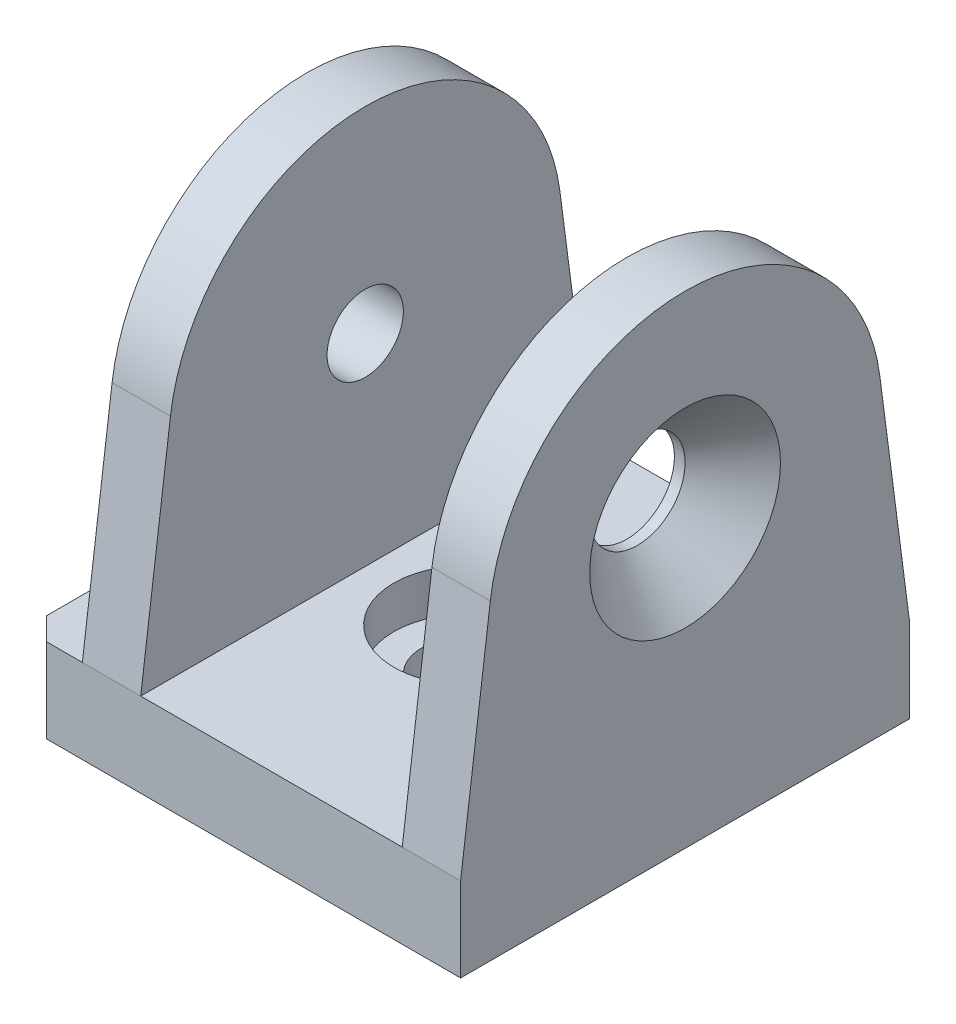
SolidWorks part; units mm, degrees
material "Алюминиевый сплав"
ref_plane "Спереди" through (0, 0, 0) normal (0, 0, 1) x (1, 0, 0)
ref_plane "Сверху" through (0, 0, 0) normal (0, 1, 0) x (1, 0, 0)
ref_plane "Справа" through (0, 0, 0) normal (1, 0, 0) x (0, 0, -1)
sketch "Эскиз1" plane through (0, 0, 0) normal (0, 1, 0) x (1, 0, 0)
  line L1 (19.45, -20) -> (-19.45, -20)
  line L2 (19.45, -20) -> (19.45, 20)
  line L3 (19.45, 20) -> (-19.45, 20)
  line L4 (-19.45, -20) -> (-19.45, 20)
  line L5 (19.45, -20) -> (-19.45, 20) construction
  line L6 (19.45, 20) -> (-19.45, -20) construction
  point P0 (0, 0)
  dimension "D1" = 38.9
  dimension "D2" = 40
extrude "Бобышка-Вытянуть1" add sketch "Эскиз1" along normal blind 7.5
sketch "Эскиз2" plane through (0, 0, 0) normal (0, 0, 1) x (1, 0, 0)
  line L1 (-19.45, 0) -> (19.45, 0) construction
  line L2 (-4, 0) -> (-4, 3.75)
  line L3 (-4, 3.75) -> (-6.5, 3.75)
  line L4 (-6.5, 3.75) -> (-6.5, 7.5)
  line L5 (-19.45, 7.5) -> (19.45, 7.5) construction
  line L7 (0, 7.5) -> (0, 0) construction
  line L11 (-19.45, 7.5) -> (-19.45, 0) construction
  line L12 (-6.5, 7.5) -> (0, 7.5)
  line L13 (0, 0) -> (-4, 0)
  line L14 (0, 0) -> (0, 7.5)
  point P17 (-19.45, 3.75)
  dimension "D1" = 8
  dimension "D2" = 13
revolve "Вырез-Повернуть1" cut sketch "Эскиз2" angle 360 about L7
sketch "Эскиз3" plane through (19.45, 0, 0) normal (1, 0, 0) x (0, 0, -1)
  line L0 (-20, 7.5) -> (-17.3526, 27.7667)
  line L1 (17.3526, 27.7667) -> (20, 7.5)
  line L2 (20, 7.5) -> (-20, 7.5)
  line L3 (-20, 0) -> (20, 0) construction
  arc A0 (-17.3526, 27.7667) -> (17.3526, 27.7667) centre (0, 25.5) cw
  dimension "D1" = 43
  dimension "D2" = 18
extrude "Бобышка-Вытянуть2" add sketch "Эскиз3" against normal blind 33.7
sketch "Эскиз4" plane through (0, 0, 0) normal (0, 0, 1) x (1, 0, 0)
  line L0 (-14.25, 7.5) -> (19.45, 7.5) construction
  line L1 (14.25, 7.5) -> (-9.05, 7.5)
  line L2 (14.25, 7.5) -> (14.25, 43)
  line L3 (14.25, 43) -> (-9.05, 43)
  line L4 (-9.05, 7.5) -> (-9.05, 43)
  line L5 (19.45, 43) -> (-14.25, 43) construction
  line L6 (14.25, 25.25) -> (19.45, 25.25) construction
  line L7 (19.45, 27.7667) -> (19.45, 7.5) construction
  line L8 (-9.05, 25.25) -> (-14.25, 25.25) construction
  line L9 (-14.25, 27.7667) -> (-14.25, 7.5) construction
  dimension "D1" = 5.2
extrude "Вырез-Вытянуть1" cut sketch "Эскиз4" against normal through all and the other way through all
chamfer "Фаска1" distance 2 angle 45 2 edges at (-19.45, 3.75, -20) (-19.45, 3.75, 20)
hole_wizard "Зенковка для винта с полупотайной головкой M81" positions "Эскиз8" profile "Эскиз10" countersink size "M8" standard "ISO" end condition up to next
sketch "Эскиз8" plane through (19.45, 0, 0) normal (1, 0, 0) x (0, 0, -1)
  point P0 (0, 25.5)
sketch "Эскиз10" plane through (19.45, 25.5, 0) normal (0, 1, 0) x (0, 0, -1)
  line L0 (0, 0) -> (0, 5.2)
  line L1 (0, 5.2) -> (4.25, 5.2)
  line L2 (4.25, 5.2) -> (4.25, 4.25)
  line L3 (4.25, 4.25) -> (8.5, 0)
  line L5 (8.5, 0) -> (0, 0)
  line L6 (-4.25, 4.25) -> (-8.5, 0) construction
  line L11 (0, -6.35) -> (0, 107.95) construction
  dimension "Диаметр сквозного отверстия" = 8.5
  dimension "Глубина сквозного отверстия" = 5.2
  dimension "Диаметр передней зенковки" = 17
  dimension "Угол передней зенковки" = 90
hole_wizard "Отверстие обработанное метчиком M81" positions "Эскиз11" profile "Эскиз13" tap size "M8" standard "ISO" end condition up to next
sketch "Эскиз11" plane through (-14.25, 0, 0) normal (-1, 0, 0) x (0, 0, 1)
  point P0 (0, 25.5)
sketch "Эскиз13" plane through (-14.25, 25.5, 0) normal (0, 1, 0) x (0, 0, 1)
  line L0 (0, 0) -> (0, 5.2)
  line L1 (0, 5.2) -> (3.4, 5.2)
  line L2 (3.4, 5.2) -> (3.4, 0)
  line L5 (3.4, 0) -> (0, 0)
  line L11 (0, -6.35) -> (0, 107.95) construction
  dimension "Диаметр проходного сверла" = 6.8
  dimension "Глубина проходного сверла" = 5.2
cosmetic thread "Отверстие резьбы1" parameters "D2"=8
